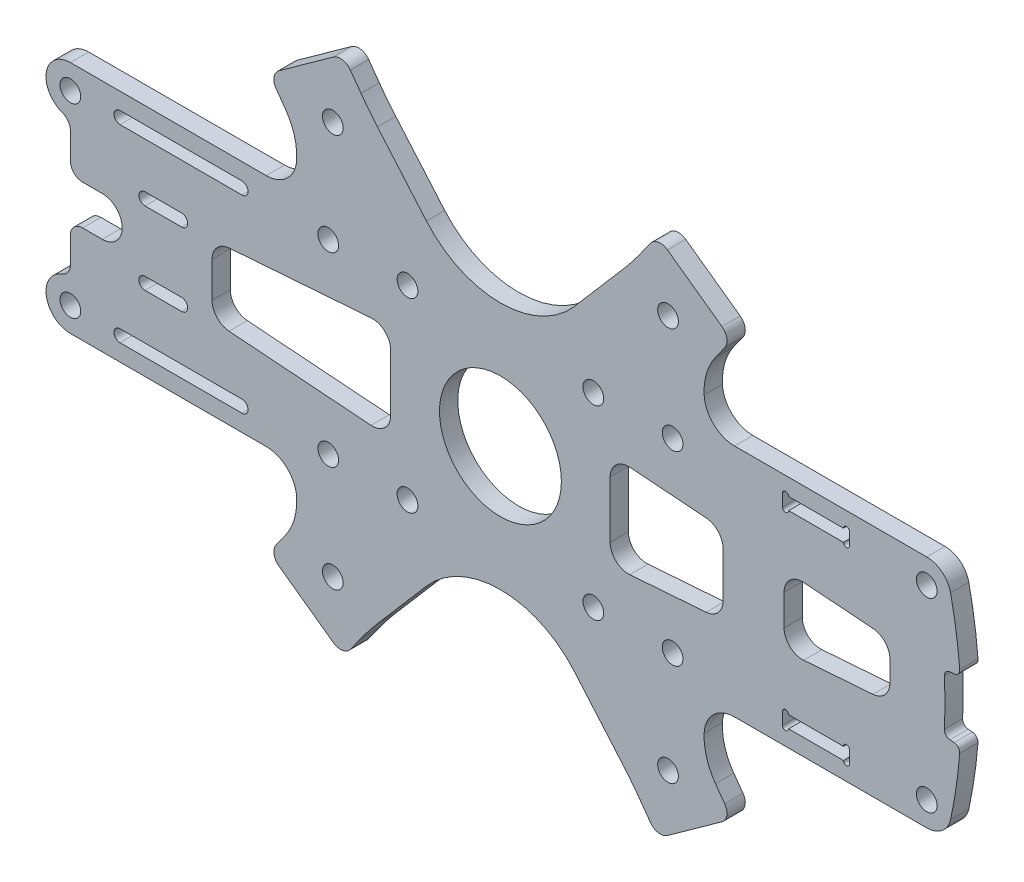
SolidWorks part; units mm, degrees
material "Thornel Mat VMA"
ref_plane "Front Plane" through (0, 0, 0) normal (0, 0, 1) x (1, 0, 0)
ref_plane "Top Plane" through (0, 0, 0) normal (0, 1, 0) x (1, 0, 0)
ref_plane "Right Plane" through (0, 0, 0) normal (1, 0, 0) x (0, 0, -1)
sketch "Sketch1" plane through (0, 0, 0) normal (0, 0, 1) x (1, 0, 0)
  line L0 (57.2807, -14.5) -> (57.2807, -16.5)
  line L1 (56.2807, -16.5) -> (47.2807, -16.5)
  line L2 (46.2807, -16.5) -> (46.2807, -14.5)
  line L3 (47.2807, -14.5) -> (56.2807, -14.5)
  line L4 (61.1287, 4.6848) -> (49.7552, 5.5246)
  line L5 (46.5343, 2.5327) -> (46.5343, -2.5327)
  line L6 (49.7552, -5.5246) -> (61.1287, -4.6848)
  line L7 (-47.316, 2.918) -> (-47.316, -2.918)
  line L8 (-44.5369, -5.9099) -> (-21.2209, -7.6314)
  line L9 (-18, -4.6395) -> (-18, 4.6395)
  line L10 (-21.2209, 7.6314) -> (-44.5369, 5.9099)
  line L11 (21.2209, 7.6314) -> (33.7552, 6.7059)
  line L12 (36.5343, 3.7141) -> (36.5343, -3.7141)
  line L13 (33.7552, -6.7059) -> (21.2209, -7.6314)
  line L14 (18, -4.6395) -> (18, 4.6395)
  line L15 (57.2807, 14.5) -> (57.2807, 16.5)
  line L16 (56.2807, 16.5) -> (47.2807, 16.5)
  line L17 (46.2807, 16.5) -> (46.2807, 14.5)
  line L18 (47.2807, 14.5) -> (56.2807, 14.5)
  line L19 (-58.316, 7) -> (-52.316, 7)
  line L20 (-52.316, 5) -> (-58.316, 5)
  line L21 (-58.316, -7) -> (-52.316, -7)
  line L22 (-52.316, -5) -> (-58.316, -5)
  line L23 (24.6144, -41.15) -> (22.8708, -38.7216)
  line L24 (20.1745, -35.2929) -> (12.1337, -25.9382)
  line L25 (-12.1337, -25.9382) -> (-20.1745, -35.2929)
  line L26 (-22.8708, -38.7216) -> (-24.6144, -41.15)
  line L27 (-27.4055, -41.608) -> (-36.3406, -35.1921)
  line L28 (-36.7986, -32.401) -> (-35.2934, -30.3048)
  line L29 (-38.4212, -19.25) -> (-70.5603, -19.25)
  line L30 (-70.5603, -9.5931) -> (-70.5603, -5.25)
  line L31 (-68.5603, -3.25) -> (-65.3092, -3.25)
  line L32 (-65.3092, 3.25) -> (-68.5603, 3.25)
  line L33 (-70.5603, 5.25) -> (-70.5603, 9.5931)
  line L34 (-70.5603, 19.25) -> (-38.4212, 19.25)
  line L35 (-35.2934, 30.3048) -> (-36.7986, 32.401)
  line L36 (-36.3406, 35.1921) -> (-27.4055, 41.608)
  line L37 (-24.6144, 41.15) -> (-22.8708, 38.7216)
  line L38 (-20.1745, 35.2929) -> (-12.1337, 25.9382)
  line L39 (12.1337, 25.9382) -> (20.1745, 35.2929)
  line L40 (22.8708, 38.7216) -> (24.6144, 41.15)
  line L41 (27.4055, 41.608) -> (36.3406, 35.1921)
  line L42 (36.7986, 32.401) -> (35.2934, 30.3048)
  line L43 (38.4212, 19.25) -> (69.9498, 19.25)
  line L44 (74.4479, 4.8846) -> (73.745, 4.8231)
  line L45 (73.745, -4.8231) -> (74.4479, -4.8846)
  line L46 (69.9498, -19.25) -> (38.4212, -19.25)
  line L47 (35.2934, -30.3048) -> (36.7986, -32.401)
  line L48 (36.3406, -35.1921) -> (27.4055, -41.608)
  line L49 (-42.4052, -14.5) -> (-62.4052, -14.5)
  line L50 (-62.4052, -16.5) -> (-42.4052, -16.5)
  line L51 (-42.4052, 14.5) -> (-62.4052, 14.5)
  line L52 (-62.4052, 16.5) -> (-42.4052, 16.5)
  circle A3 centre (0, 0) radius 10
  arc A21 (57.2807, -14.5) -> (56.2807, -14.5) centre (56.7807, -14.5) ccw
  arc A22 (56.2807, -16.5) -> (57.2807, -16.5) centre (56.7807, -16.5) ccw
  arc A23 (46.2807, -16.5) -> (47.2807, -16.5) centre (46.7807, -16.5) ccw
  arc A24 (47.2807, -14.5) -> (46.2807, -14.5) centre (46.7807, -14.5) ccw
  arc A25 (49.7552, 5.5246) -> (46.5343, 2.5327) centre (49.5343, 2.5327) ccw
  arc A26 (46.5343, -2.5327) -> (49.7552, -5.5246) centre (49.5343, -2.5327) ccw
  arc A27 (61.1287, -4.6848) -> (63.9066, -1.7763) centre (60.9078, -1.693) ccw
  arc A28 (63.9066, -1.7763) -> (63.9066, 1.7763) centre (0, 0) ccw
  arc A29 (63.9066, 1.7763) -> (61.1287, 4.6848) centre (60.9078, 1.693) ccw
  arc A30 (-44.5369, 5.9099) -> (-47.316, 2.918) centre (-44.316, 2.918) ccw
  arc A31 (-47.316, -2.918) -> (-44.5369, -5.9099) centre (-44.316, -2.918) ccw
  arc A32 (-21.2209, -7.6314) -> (-18, -4.6395) centre (-21, -4.6395) ccw
  arc A33 (-18, 4.6395) -> (-21.2209, 7.6314) centre (-21, 4.6395) ccw
  arc A34 (21.2209, 7.6314) -> (18, 4.6395) centre (21, 4.6395) ccw
  arc A35 (36.5343, 3.7141) -> (33.7552, 6.7059) centre (33.5343, 3.7141) ccw
  arc A36 (33.7552, -6.7059) -> (36.5343, -3.7141) centre (33.5343, -3.7141) ccw
  arc A37 (18, -4.6395) -> (21.2209, -7.6314) centre (21, -4.6395) ccw
  arc A38 (56.2807, 14.5) -> (57.2807, 14.5) centre (56.7807, 14.5) ccw
  arc A39 (57.2807, 16.5) -> (56.2807, 16.5) centre (56.7807, 16.5) ccw
  arc A40 (47.2807, 16.5) -> (46.2807, 16.5) centre (46.7807, 16.5) ccw
  arc A41 (46.2807, 14.5) -> (47.2807, 14.5) centre (46.7807, 14.5) ccw
  arc A42 (-58.316, 7) -> (-59.316, 6) centre (-58.316, 6) ccw
  arc A43 (-52.316, 5) -> (-52.316, 7) centre (-52.316, 6) ccw
  arc A44 (-59.316, 6) -> (-58.316, 5) centre (-58.316, 6) ccw
  arc A45 (-59.316, -6) -> (-58.316, -7) centre (-58.316, -6) ccw
  arc A46 (-52.316, -7) -> (-52.316, -5) centre (-52.316, -6) ccw
  arc A47 (-58.316, -5) -> (-59.316, -6) centre (-58.316, -6) ccw
  arc A48 (24.6144, -41.15) -> (27.4055, -41.608) centre (26.239, -39.9834) ccw
  arc A49 (22.8708, -38.7216) -> (20.1745, -35.2929) centre (-17.7433, -67.8849) ccw
  arc A50 (12.1337, -25.9382) -> (-12.1337, -25.9382) centre (0, -36.3676) ccw
  arc A51 (-20.1745, -35.2929) -> (-22.8708, -38.7216) centre (17.7433, -67.8849) ccw
  arc A52 (-27.4055, -41.608) -> (-24.6144, -41.15) centre (-26.239, -39.9834) ccw
  arc A53 (-36.7986, -32.401) -> (-36.3406, -35.1921) centre (-35.1741, -33.5675) ccw
  arc A54 (-35.2934, -30.3048) -> (-33.4261, -24.0279) centre (-43.4163, -24.4721) ccw
  arc A55 (-33.4261, -24.0279) -> (-38.4212, -19.25) centre (-38.4212, -24.25) ccw
  arc A56 (-71.8937, -11.4788) -> (-70.5603, -19.25) centre (-70.5603, -15.25) ccw
  arc A57 (-71.8937, -11.4788) -> (-70.5603, -9.5931) centre (-72.5603, -9.5931) ccw
  arc A58 (-68.5603, -3.25) -> (-70.5603, -5.25) centre (-68.5603, -5.25) ccw
  arc A59 (-65.3092, -3.25) -> (-65.3092, 3.25) centre (-65.3092, 0) ccw
  arc A60 (-70.5603, 5.25) -> (-68.5603, 3.25) centre (-68.5603, 5.25) ccw
  arc A61 (-70.5603, 9.5931) -> (-71.8937, 11.4788) centre (-72.5603, 9.5931) ccw
  arc A62 (-70.5603, 19.25) -> (-71.8937, 11.4788) centre (-70.5603, 15.25) ccw
  arc A63 (-38.4212, 19.25) -> (-33.4261, 24.0279) centre (-38.4212, 24.25) ccw
  arc A64 (-33.4261, 24.0279) -> (-35.2934, 30.3048) centre (-43.4163, 24.4721) ccw
  arc A65 (-36.3406, 35.1921) -> (-36.7986, 32.401) centre (-35.1741, 33.5675) ccw
  arc A66 (-24.6144, 41.15) -> (-27.4055, 41.608) centre (-26.239, 39.9834) ccw
  arc A67 (-22.8708, 38.7216) -> (-20.1745, 35.2929) centre (17.7433, 67.8849) ccw
  arc A68 (-12.1337, 25.9382) -> (12.1337, 25.9382) centre (0, 36.3676) ccw
  arc A69 (20.1745, 35.2929) -> (22.8708, 38.7216) centre (-17.7433, 67.8849) ccw
  arc A70 (27.4055, 41.608) -> (24.6144, 41.15) centre (26.239, 39.9834) ccw
  arc A71 (36.7986, 32.401) -> (36.3406, 35.1921) centre (35.1741, 33.5675) ccw
  arc A72 (35.2934, 30.3048) -> (33.4261, 24.0279) centre (43.4163, 24.4721) ccw
  arc A73 (33.4261, 24.0279) -> (38.4212, 19.25) centre (38.4212, 24.25) ccw
  arc A74 (73.858, 16.102) -> (69.9498, 19.25) centre (69.9498, 15.25) ccw
  arc A75 (75.3576, 5.9597) -> (73.858, 16.102) centre (0, 0) ccw
  arc A76 (74.4479, 4.8846) -> (75.3576, 5.9597) centre (74.3607, 5.8808) ccw
  arc A77 (73.745, 4.8231) -> (72.8335, 3.7752) centre (73.8322, 3.8269) ccw
  arc A78 (72.8335, -3.7752) -> (72.8335, 3.7752) centre (0, 0) ccw
  arc A79 (72.8335, -3.7752) -> (73.745, -4.8231) centre (73.8322, -3.8269) ccw
  arc A80 (75.3576, -5.9597) -> (74.4479, -4.8846) centre (74.3607, -5.8808) ccw
  arc A81 (73.858, -16.102) -> (75.3576, -5.9597) centre (0, 0) ccw
  arc A82 (69.9498, -19.25) -> (73.858, -16.102) centre (69.9498, -15.25) ccw
  arc A83 (38.4212, -19.25) -> (33.4261, -24.0279) centre (38.4212, -24.25) ccw
  arc A84 (33.4261, -24.0279) -> (35.2934, -30.3048) centre (43.4163, -24.4721) ccw
  arc A85 (36.3406, -35.1921) -> (36.7986, -32.401) centre (35.1741, -33.5675) ccw
  arc A86 (-42.4052, -16.5) -> (-42.4052, -14.5) centre (-42.4052, -15.5) ccw
  arc A87 (-62.4052, -14.5) -> (-62.4052, -16.5) centre (-62.4052, -15.5) ccw
  arc A88 (-42.4052, 14.5) -> (-42.4052, 16.5) centre (-42.4052, 15.5) ccw
  arc A89 (-62.4052, 16.5) -> (-62.4052, 14.5) centre (-62.4052, 15.5) ccw
  dimension "D1" = 20
extrude "Boss-Extrude1" add sketch "Sketch1" along normal blind 3
hole_wizard "M3 Clearance Hole1" positions "Sketch4" profile "Sketch5" hole size "M3" standard "ANSI Metric" end condition up to next
sketch "Sketch4" plane through (0, 0, 3) normal (0, 0, 1) x (1, 0, 0)
  line L0 (-70.5603, 15.25) -> (69.9498, 15.25) construction
  line L2 (-27.4986, 32.3079) -> (-15.25, 15.25) construction
  line L4 (15.25, 15.25) -> (27.4986, 32.3079) construction
  line L7 (0, 0) -> (50000, 0) construction
  line L8 (15.25, -15.25) -> (27.4986, -32.3079) construction
  line L9 (-27.4986, -32.3079) -> (-15.25, -15.25) construction
  line L10 (-70.5603, -15.25) -> (69.9498, -15.25) construction
  arc A0 (73.858, 16.102) -> (69.9498, 19.25) centre (69.9498, 15.25) ccw construction
  arc A1 (-70.5603, 19.25) -> (-71.8937, 11.4788) centre (-70.5603, 15.25) ccw construction
  point P2 (-70.5603, 15.25)
  point P5 (-28.25, 15.25)
  point P8 (-15.25, 15.25)
  point P11 (15.25, 15.25)
  point P14 (28.25, 15.25)
  point P17 (69.9498, 15.25)
  point P42 (27.4986, 32.3079)
  point P45 (-27.4986, 32.3079)
  point P156 (15.25, -15.25)
  point P157 (27.4986, -32.3079)
  point P158 (-27.4986, -32.3079)
  point P159 (-15.25, -15.25)
  point P160 (-70.5603, -15.25)
  point P161 (69.9498, -15.25)
  point P162 (28.25, -15.25)
  point P163 (-28.25, -15.25)
  dimension "D1" = 42.3103
  dimension "D2" = 13
  dimension "D3" = 30.5
  dimension "D4" = 13
  dimension "D5" = 54.319
  dimension "D6" = 21
  dimension "D7" = 54.319
sketch "Sketch5" plane through (-70.5603, 15.25, 3) normal (1, 0, 0) x (0, -1, 0)
  line L0 (0, 0) -> (0, 3)
  line L1 (0, 3) -> (1.7, 3)
  line L2 (1.7, 3) -> (1.7, 0)
  line L5 (1.7, 0) -> (0, 0)
  line L11 (0, -6.35) -> (0, 107.95) construction
  dimension "Thru Hole Dia." = 3.4
  dimension "Thru Hole Depth" = 3
